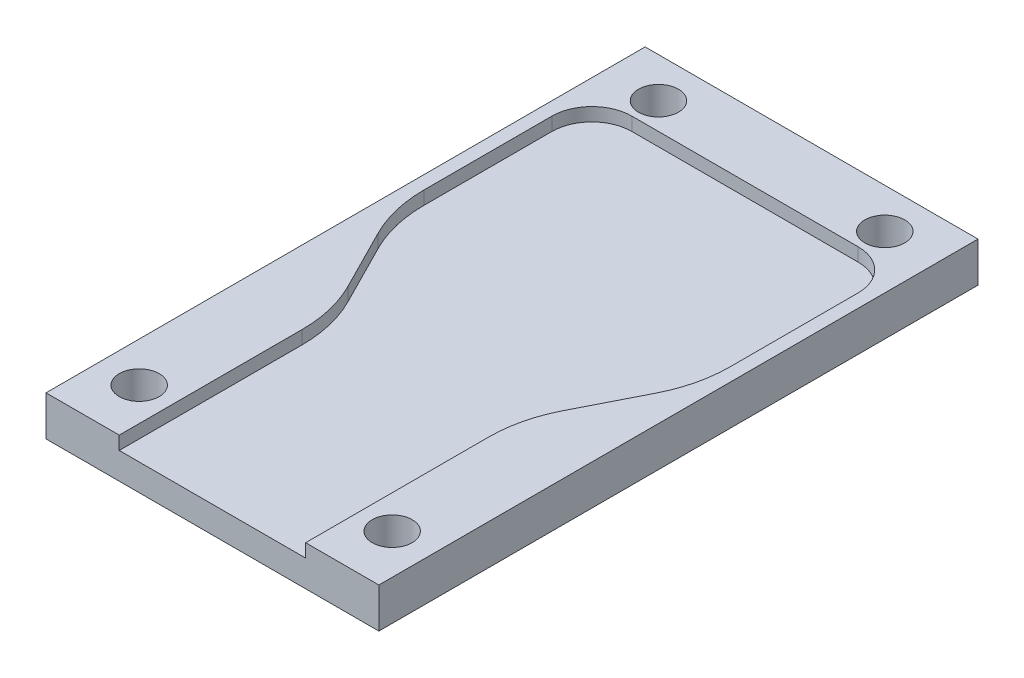
SolidWorks part; units mm, degrees
ref_plane "Front Plane" through (0, 0, 0) normal (0, 0, 1) x (1, 0, 0)
ref_plane "Top Plane" through (0, 0, 0) normal (0, 1, 0) x (1, 0, 0)
ref_plane "Right Plane" through (0, 0, 0) normal (1, 0, 0) x (0, 0, -1)
sketch "Sketch1" plane through (0, 0, 0) normal (0, 1, 0) x (1, 0, 0)
  line L1 (0, 0) -> (25, 0)
  line L2 (0, 0) -> (0, 45)
  line L3 (0, 45) -> (25, 45)
  line L4 (25, 0) -> (25, 45)
  dimension "D1" = 25
  dimension "D2" = 45
extrude "Boss-Extrude1" add sketch "Sketch1" along normal blind 3
sketch "Sketch2" plane through (0, 3, 0) normal (0, 1, 0) x (1, 0, 0)
  line L0 (25, 0) -> (25, 45) construction
  line L1 (4, 40) -> (21, 40)
  line L2 (1, 37) -> (1, 27.3904)
  line L4 (24, 37) -> (24, 27.3904)
  line L5 (0, 45) -> (0, 0) construction
  line L6 (5.5, 13.7348) -> (5.5, 0)
  line L7 (0, 0) -> (25, 0) construction
  line L8 (19.5, 13.7348) -> (19.5, 0)
  line L9 (25, 45) -> (0, 45) construction
  line L11 (22.919, 22.868) -> (20.581, 18.2572)
  line L12 (2.081, 22.868) -> (4.419, 18.2572)
  line L15 (0, 45) -> (0, 0)
  line L16 (0, 0) -> (25, 0)
  line L17 (25, 0) -> (25, 45)
  line L18 (25, 45) -> (0, 45)
  line L20 (5.5, 0) -> (19.5, 0)
  arc A2 (24, 37) -> (21, 40) centre (21, 37) ccw
  arc A3 (4, 40) -> (1, 37) centre (4, 37) ccw
  arc A4 (2.081, 22.868) -> (1, 27.3904) centre (11, 27.3904) cw
  arc A5 (4.419, 18.2572) -> (5.5, 13.7348) centre (-4.5, 13.7348) cw
  arc A6 (20.581, 18.2572) -> (19.5, 13.7348) centre (29.5, 13.7348) ccw
  arc A7 (22.919, 22.868) -> (24, 27.3904) centre (14, 27.3904) ccw
  point P8 (0, 0)
  point P12 (0, 0)
  point P19 (19.5, 25)
  point P21 (5.5, 16.1252)
  point P34 (19.5, 16.1252)
  dimension "D7" = 16.1252
  dimension "D8" = 3
  dimension "D10" = 10
  dimension "D1" = 1
  dimension "D2" = 1
  dimension "D3" = 14
  dimension "D4" = 5.5
  dimension "D5" = 16.1252
  dimension "D6" = 5
  dimension "D9" = 0
extrude "Cut-Extrude1" cut sketch "Sketch2" against normal blind 1 contours L4 A7 L11 A6 L8 L20 L6 A5 L12 A4 L2 A3 L1 A2
sketch "Sketch3" plane through (0, 3, 0) normal (0, 1, 0) x (1, 0, 0)
  line L0 (19.5, 0) -> (25, 0) construction
  line L1 (25, 0) -> (25, 45) construction
  line L2 (0, 0) -> (5.5, 0) construction
  line L3 (0, 45) -> (0, 0) construction
  line L4 (25, 45) -> (0, 45) construction
  circle A0 centre (21, 42) radius 1.5
  circle A1 centre (4, 42) radius 1.5
  circle A2 centre (3, 4) radius 1.5
  circle A3 centre (22, 4) radius 1.5
  point P16 (0, 0)
  point P17 (0, 0)
  point P18 (0, 0)
  dimension "D1" = 3
  dimension "D2" = 3
  dimension "D3" = 3
  dimension "D4" = 3
  dimension "D5" = 4
  dimension "D6" = 3
  dimension "D7" = 4
  dimension "D8" = 3
  dimension "D9" = 3
  dimension "D10" = 4
  dimension "D11" = 3
  dimension "D12" = 4
extrude "Cut-Extrude2" cut sketch "Sketch3" against normal through all
